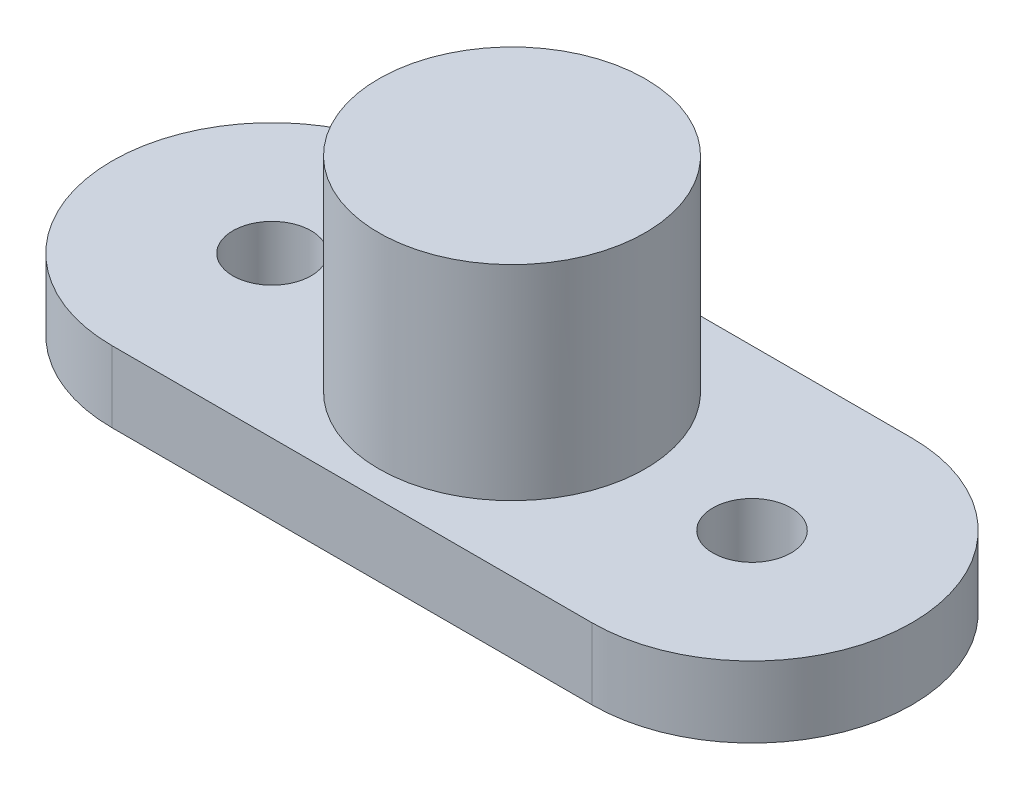
SolidWorks part; units mm, degrees
ref_plane "Front Plane" through (0, 0, 0) normal (0, 0, 1) x (1, 0, 0)
ref_plane "Top Plane" through (0, 0, 0) normal (0, 1, 0) x (1, 0, 0)
ref_plane "Right Plane" through (0, 0, 0) normal (1, 0, 0) x (0, 0, -1)
sketch "Sketch1" plane through (0, 0, 0) normal (0, 1, 0) x (1, 0, 0)
  line L0 (0, 0) -> (6.75, 0)
  line L1 (0, 0) -> (-6.75, 0)
  line L2 (-6.75, 4.4995) -> (6.75, 4.4995)
  line L3 (-6.75, -4.4995) -> (6.75, -4.4995)
  circle A0 centre (-6.75, 0) radius 1.1
  circle A1 centre (6.75, 0) radius 1.1
  arc A2 (6.75, 4.4995) -> (6.75, -4.4995) centre (6.75, 0) cw
  arc A3 (-6.75, 4.4995) -> (-6.75, -4.4995) centre (-6.75, 0) ccw
  circle A6 centre (0, 0) radius 3.75
extrude "Boss-Extrude3" add sketch "Sketch1" along normal blind 2
sketch "Sketch3" plane through (0, 0, 0) normal (0, -1, 0) x (1, 0, 0)
  circle A2 centre (0, 0) radius 3.75
extrude "Boss-Extrude4" add sketch "Sketch3" against normal blind 7.75
